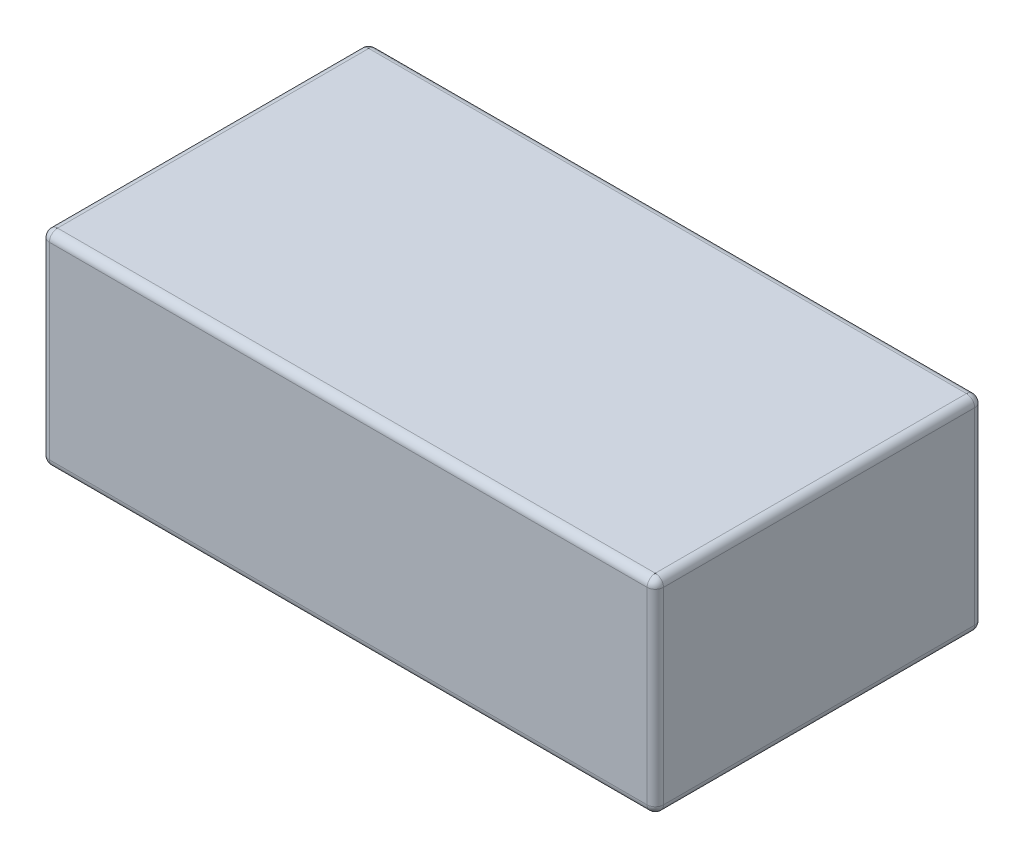
SolidWorks part; units mm, degrees
ref_plane "Front Plane" through (0, 0, 0) normal (0, 0, 1) x (1, 0, 0)
ref_plane "Top Plane" through (0, 0, 0) normal (0, 1, 0) x (1, 0, 0)
ref_plane "Right Plane" through (0, 0, 0) normal (1, 0, 0) x (0, 0, -1)
sketch "Sketch1" plane through (0, 0, 0) normal (0, 1, 0) x (1, 0, 0)
  line L1 (-0.73, -0.4) -> (0.73, -0.4)
  line L2 (-0.75, -0.38) -> (-0.75, 0.38)
  line L3 (-0.73, 0.4) -> (0.73, 0.4)
  line L4 (0.75, -0.38) -> (0.75, 0.38)
  line L5 (-0.75, -0.4) -> (0.75, 0.4) construction
  line L6 (-0.75, 0.4) -> (0.75, -0.4) construction
  arc A4 (-0.75, -0.38) -> (-0.73, -0.4) centre (-0.73, -0.38) ccw
  arc A5 (0.73, -0.4) -> (0.75, -0.38) centre (0.73, -0.38) ccw
  arc A6 (0.75, 0.38) -> (0.73, 0.4) centre (0.73, 0.38) ccw
  arc A7 (-0.73, 0.4) -> (-0.75, 0.38) centre (-0.73, 0.38) ccw
  point P0 (0, 0)
  dimension "D4" = 0.02
  dimension "D1" = 1.5
  dimension "D2" = 0.8
extrude "Boss-Extrude1" add sketch "Sketch1" along normal mid plane 0.5
fillet "Fillet1" [suppressed] radius 0.02
fillet "Fillet2" radius 0.02 16 edges at (-0.75, 0.25, 0) (-0.7441, 0.25, -0.3941) (0, 0.25, -0.4) (0.7441, 0.25, -0.3941) (0.75, 0.25, 0) (0.7441, 0.25, 0.3941) (0, 0.25, 0.4) (-0.7441, 0.25, 0.3941) (0, -0.25, 0.4) (0.7441, -0.25, 0.3941) (0.75, -0.25, 0) (0.7441, -0.25, -0.3941) (0, -0.25, -0.4) (-0.7441, -0.25, -0.3941) (-0.75, -0.25, 0) (-0.7441, -0.25, 0.3941)
